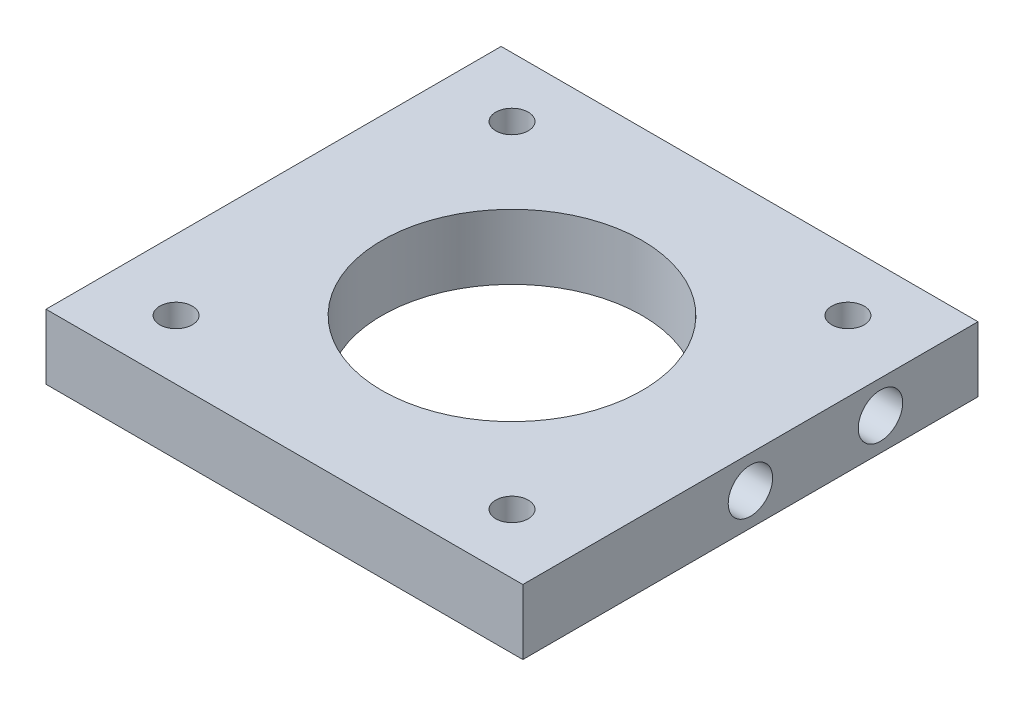
SolidWorks part; units mm, degrees
ref_plane "Front" through (0, 0, 0) normal (0, 0, 1) x (1, 0, 0)
ref_plane "Top" through (0, 0, 0) normal (0, 1, 0) x (1, 0, 0)
ref_plane "Right" through (0, 0, 0) normal (1, 0, 0) x (0, 0, -1)
sketch "Sketch1" plane through (0, 0, 0) normal (0, 0, 1) x (1, 0, 0)
  line L6 (-22, -3) -> (22, -3)
  line L9 (-22, -3) -> (-22, 3)
  line L10 (-22, 3) -> (22, 3)
  line L11 (22, -3) -> (22, 3)
  line L12 (-22, -3) -> (22, 3) construction
  line L13 (-22, 3) -> (22, -3) construction
  point P0 (0, 0)
  dimension "D1" = 6
  dimension "D2" = 44
extrude "Boss-Extrude1" add sketch "Sketch1" along normal blind 42
sketch "Sketch5" plane through (0, 3, 0) normal (0, 1, 0) x (1, 0, 0)
  line L0 (-22, -42) -> (22, 0) construction
  line L2 (-15.5, -5.5) -> (15.5, -5.5) construction
  line L3 (-15.5, -5.5) -> (-15.5, -36.5) construction
  line L4 (-15.5, -36.5) -> (15.5, -36.5) construction
  line L5 (15.5, -5.5) -> (15.5, -36.5) construction
  line L6 (-15.5, -5.5) -> (15.5, -36.5) construction
  line L7 (-15.5, -36.5) -> (15.5, -5.5) construction
  circle A0 centre (0, -21) radius 12
  circle A1 centre (-15.5, -5.5) radius 1.5
  circle A2 centre (15.5, -5.5) radius 1.5
  circle A3 centre (15.5, -36.5) radius 1.5
  circle A4 centre (-15.5, -36.5) radius 1.5
  dimension "D1" = 24
  dimension "D3" = 3
  dimension "D4" = 3
  dimension "D5" = 3
  dimension "D6" = 3
  dimension "D2" = 31
extrude "Cut-Extrude4" cut sketch "Sketch5" against normal up to next
sketch "Sketch6" plane through (-22, 0, 0) normal (-1, 0, 0) x (0, 0, 1)
  line L0 (21, 3) -> (21, -3) construction
  line L1 (42, 3) -> (0, 3) construction
  line L2 (42, -3) -> (0, -3) construction
  circle A0 centre (9, 0) radius 2.05
  circle A1 centre (21, 0) radius 2.05
  dimension "D1" = 4.1
  dimension "D2" = 4.1
  dimension "D3" = 12
extrude "Cut-Extrude5" cut sketch "Sketch6" against normal blind 6
sketch "Sketch7" plane through (22, 0, 0) normal (1, 0, 0) x (0, 0, -1)
  circle A0 centre (-9, 0) radius 2.05 construction
  circle A1 centre (-21, 0) radius 2.05 construction
  circle A2 centre (-9, 0) radius 2.05
  circle A3 centre (-21, 0) radius 2.05
extrude "Cut-Extrude6" cut sketch "Sketch7" against normal blind 6
